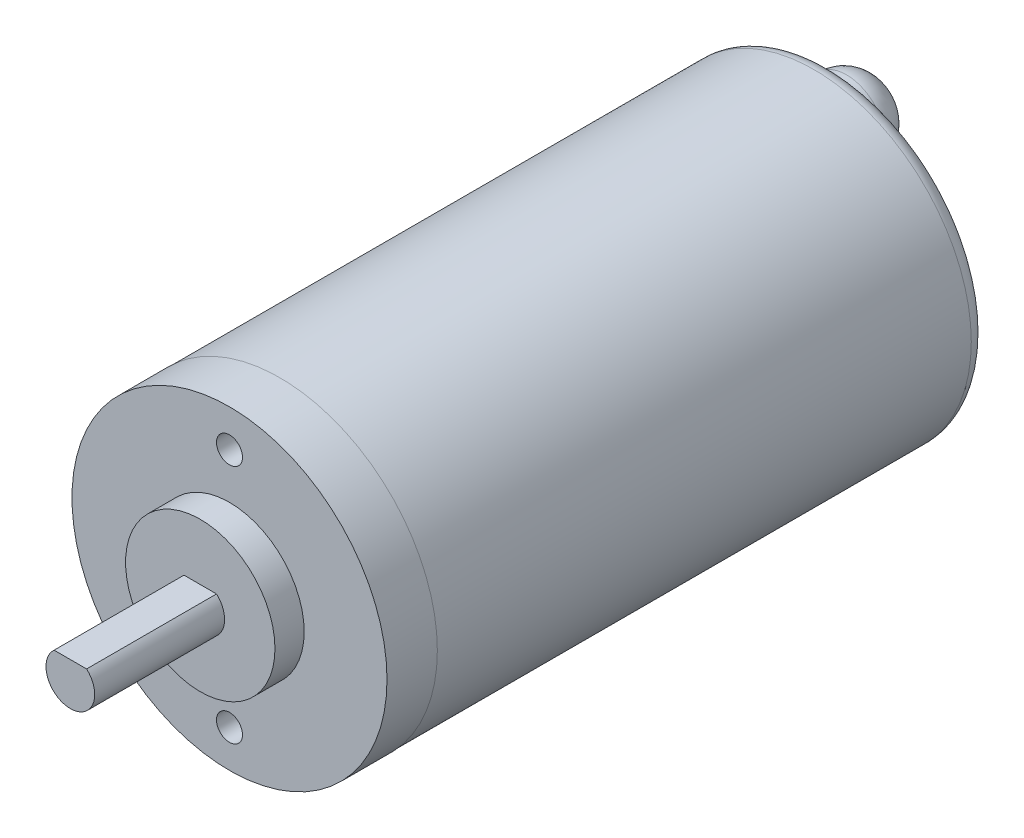
SolidWorks part; units mm, degrees
ref_plane "Front Plane" through (0, 0, 0) normal (0, 0, 1) x (1, 0, 0)
ref_plane "Top Plane" through (0, 0, 0) normal (0, 1, 0) x (1, 0, 0)
ref_plane "Right Plane" through (0, 0, 0) normal (1, 0, 0) x (0, 0, -1)
sketch "Sketch1" plane through (0, 0, 0) normal (0, 0, 1) x (1, 0, 0)
  circle A0 centre (0, 0) radius 12.319
  dimension "D1" = 24.638
extrude "Boss-Extrude1" add sketch "Sketch1" against normal blind 46.99
sketch "Sketch2" plane through (0, 0, 0) normal (0, 0, 1) x (1, 0, 0)
  circle A0 centre (0, 0) radius 5.842
  dimension "D1" = 11.684
extrude "Boss-Extrude2" add sketch "Sketch2" along normal blind 2.286
sketch "Sketch3" plane through (0, 0, 2.286) normal (0, 0, 1) x (1, 0, 0)
  circle A0 centre (0, 0) radius 1.905
  dimension "D1" = 3.81
extrude "Boss-Extrude3" add sketch "Sketch3" along normal blind 10.16
sketch "Sketch4" plane through (0, 0, 0) normal (1, 0, 0) x (0, 0, -1)
  line L0 (46.99, -12.319) -> (46.99, 12.319) construction
  line L1 (3.937, 12.319) -> (46.99, 12.319)
  line L2 (3.937, 12.319) -> (3.937, 12.2936)
  line L3 (3.937, 12.2936) -> (46.99, 12.2936)
  line L4 (46.99, 12.319) -> (46.99, 12.2936)
  line L5 (0, 12.319) -> (0, -12.319) construction
  line L6 (46.99, 12.319) -> (0, 12.319) construction
  dimension "D1" = 3.937
  dimension "D2" = 0.0254
ref_axis "Axis1" through (0, 0, -46.99) along (0, 0, 1)
revolve "Cut-Revolve1" cut sketch "Sketch4" angle 360 about axis through (0, 0, -46.99) along (0, 0, 1)
fillet "Fillet1" radius 1.27 1 edges at (-12.2936, 0, -46.99)
sketch "Sketch5" plane through (0, 0, -46.99) normal (0, 0, -1) x (-1, 0, 0)
  circle A0 centre (0, 7.62) radius 3.048
  dimension "D1" = 6.096
  dimension "D2" = 7.62
extrude "Boss-Extrude4" add sketch "Sketch5" along normal blind 3.81
fillet "Fillet2" radius 2.54 1 edges at (-3.048, 7.62, -50.8)
sketch "Sketch6" plane through (0, 0, 0) normal (0, 0, 1) x (1, 0, 0)
  circle A0 centre (0, 9.398) radius 1.016
  circle A1 centre (0, 0) radius 5.842 construction
  dimension "D1" = 2.032
  dimension "D2" = 9.398
extrude "Cut-Extrude1" cut sketch "Sketch6" against normal blind 6.35
mirror "Mirror1" about plane through (0, 0, 0) normal (0, 1, 0) of "Cut-Extrude1"
sketch "Sketch7" plane through (0, 0, 12.446) normal (0, 0, 1) x (1, 0, 0)
  line L0 (-1.4956, 1.4181) -> (1.4956, 1.4181)
  line L3 (-1.4956, 1.4181) -> (-1.4956, 1.9261)
  line L4 (-1.4956, 1.9261) -> (1.4956, 1.9261)
  line L5 (1.4956, 1.4181) -> (1.4956, 1.9261)
  dimension "D1" = 0.508
extrude "Cut-Extrude2" cut sketch "Sketch7" against normal up to surface (10.16 mm away) up to face at (1.905, 0, 2.286)
